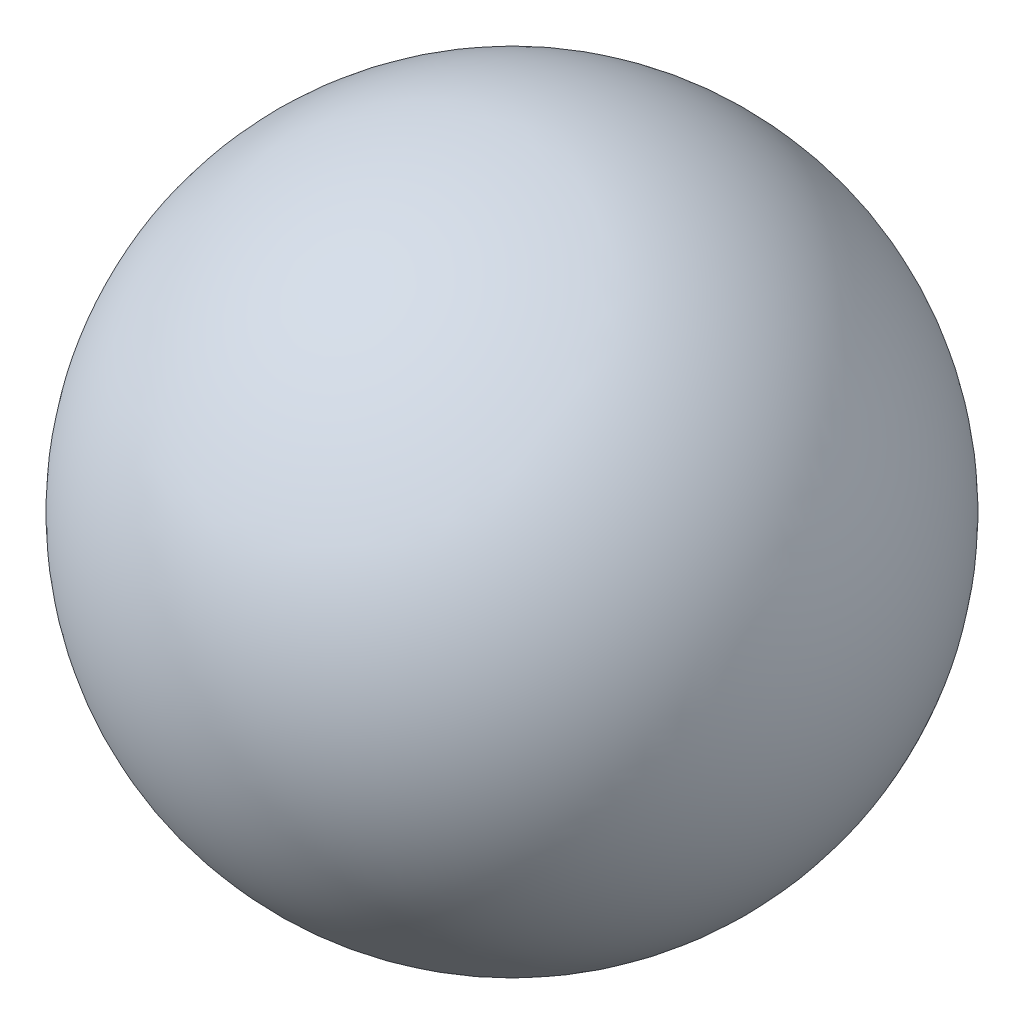
SolidWorks part; units mm, degrees
material "BUTYL"
ref_plane "Front Plane" through (0, 0, 0) normal (0, 0, 1) x (1, 0, 0)
ref_plane "Top Plane" through (0, 0, 0) normal (0, 1, 0) x (1, 0, 0)
ref_plane "Right Plane" through (0, 0, 0) normal (1, 0, 0) x (0, 0, -1)
sketch "Sketch1" plane through (0, 0, 0) normal (0, 1, 0) x (1, 0, 0)
  line L0 (0, 30) -> (0, -30)
  arc A0 (0, -30) -> (0, 30) centre (0, 0) ccw
  dimension "D1" = 60
revolve "Revolve1" add sketch "Sketch1" angle 360 about L0
sketch "Sketch2" plane through (0, 0, 0) normal (1, 0, 0) x (0, 0, -1)
  circle A0 centre (0, 0) radius 12.5
  dimension "D1" = 25
extrude "Cut-Extrude1" cut sketch "Sketch2" against normal through all
